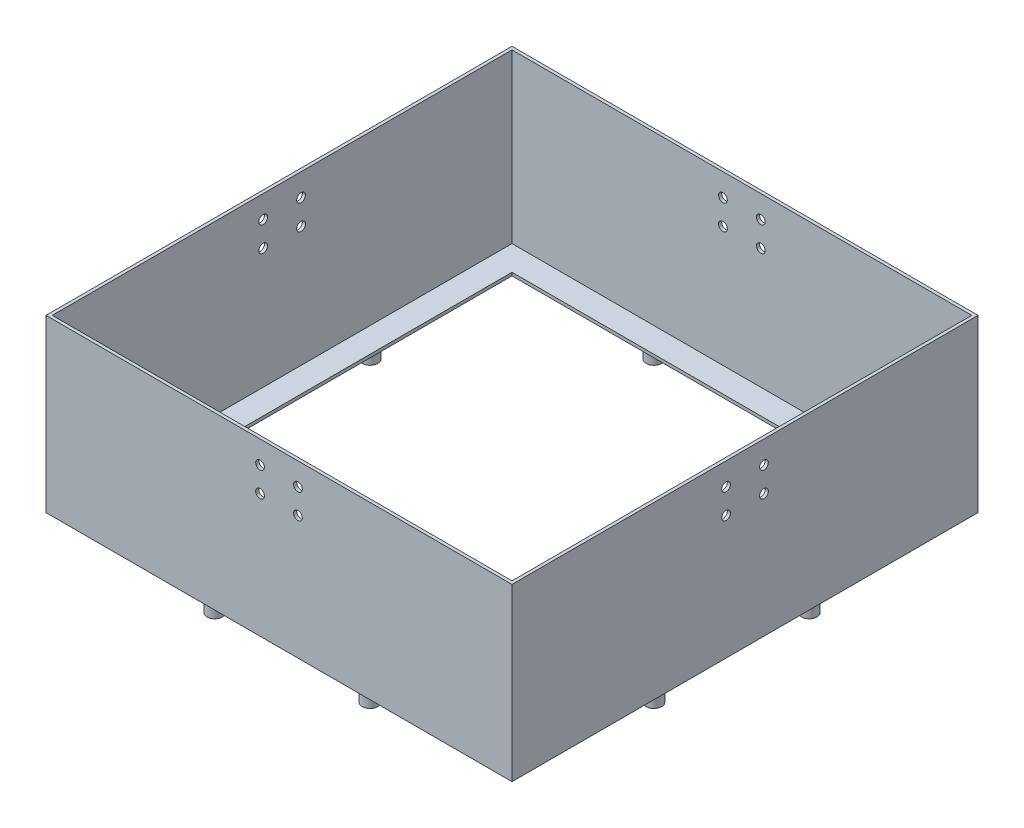
SolidWorks part; units mm, degrees
ref_plane "Front" through (0, 0, 0) normal (0, 0, 1) x (1, 0, 0)
ref_plane "Top" through (0, 0, 0) normal (0, 1, 0) x (1, 0, 0)
ref_plane "Right" through (0, 0, 0) normal (1, 0, 0) x (0, 0, -1)
sketch "Sketch1" plane through (0, 0, 0) normal (0, 1, 0) x (1, 0, 0)
  line L1 (-75, -75) -> (75, -75)
  line L2 (-75, -75) -> (-75, 75)
  line L3 (-75, 75) -> (75, 75)
  line L4 (75, -75) -> (75, 75)
  line L5 (-75, -75) -> (75, 75) construction
  line L6 (-75, 75) -> (75, -75) construction
  point P0 (0, 0)
  dimension "D1" = 150
  dimension "D2" = 150
extrude "Boss-Extrude1" add sketch "Sketch1" against normal blind 55
sketch "Sketch2" plane through (0, 0, 0) normal (0, 1, 0) x (1, 0, 0)
  line L1 (-74, -74) -> (74, -74)
  line L2 (-74, -74) -> (-74, 74)
  line L3 (-74, 74) -> (74, 74)
  line L4 (74, -74) -> (74, 74)
  line L5 (-74, -74) -> (74, 74) construction
  line L6 (-74, 74) -> (74, -74) construction
  point P0 (0, 0)
  dimension "D1" = 148
  dimension "D2" = 148
extrude "Cut-Extrude1" cut sketch "Sketch2" against normal blind 54
sketch "Sketch3" plane through (0, -54, 0) normal (0, 1, 0) x (1, 0, 0)
  line L1 (-66, -66) -> (66, -66)
  line L2 (-66, -66) -> (-66, 66)
  line L3 (-66, 66) -> (66, 66)
  line L4 (66, -66) -> (66, 66)
  line L5 (-66, -66) -> (66, 66) construction
  line L6 (-66, 66) -> (66, -66) construction
  point P0 (0, 0)
  dimension "D1" = 132
  dimension "D2" = 132
extrude "Cut-Extrude2" cut sketch "Sketch3" against normal through all
sketch "Sketch4" plane through (0, 0, -74) normal (0, 0, 1) x (1, 0, 0)
  line L3 (74, 0) -> (-74, 0) construction
  line L4 (-3.5, -17.47) -> (1.5, -17.47)
  line L5 (-3.5, -17.47) -> (-3.5, 0)
  line L6 (-3.5, 0) -> (1.5, 0)
  line L7 (1.5, -17.47) -> (1.5, 0)
  line L8 (-3.5, -17.47) -> (1.5, 0) construction
  line L9 (-3.5, 0) -> (1.5, -17.47) construction
  point P6 (-1, -8.735)
  dimension "D1" = 5
ref_axis "Axis1" through (0, 0, 0) along (0, 1, 0)
sketch "Sketch6" plane through (0, -55, 0) normal (0, -1, 0) x (1, 0, 0)
  line L0 (75, -75) -> (-75, -75) construction
  line L1 (-75, 75) -> (75, 75) construction
  circle A0 centre (-70.6782, -25) radius 2.5
  circle A1 centre (-70.6782, 25) radius 2.5
  circle A2 centre (25, 70.6782) radius 2.5
  circle A3 centre (-25, 70.6782) radius 2.5
  circle A4 centre (70.6782, -25) radius 2.5
  circle A5 centre (70.6782, 25) radius 2.5
  circle A6 centre (-25, -70.6782) radius 2.5
  circle A7 centre (25, -70.6782) radius 2.5
  dimension "D1" = 5
  dimension "D3" = 5
  dimension "D2" = 50
  dimension "D4" = 50
  dimension "D5" = 4
extrude "Boss-Extrude5" add sketch "Sketch6" along normal blind 5
sketch "Sketch9" plane through (-75, 0, 0) normal (-1, 0, 0) x (0, 0, 1)
  line L0 (-75, 0) -> (75, 0) construction
  line L1 (0, 0) -> (7.5, 0)
  line L7 (0, 0) -> (-7.5, 0)
  circle A0 centre (-6.1, -7.25) radius 1.4
  circle A1 centre (6.1, -7.25) radius 1.4
  circle A2 centre (6.1, -15.25) radius 1.4
  circle A3 centre (-6.1, -15.25) radius 1.4
  dimension "D4" = 2.8
  dimension "D2" = 7.5
  dimension "D3" = 7.5
  dimension "D5" = 7.25
extrude "Cut-Extrude4" cut sketch "Sketch9" against normal blind 10 contours A0 | A1 | A2 | A3
pattern_circular "CirPattern1" count 4 over 360 about axis through (0, 0, 0) along (0, 1, 0) of "Cut-Extrude4"
